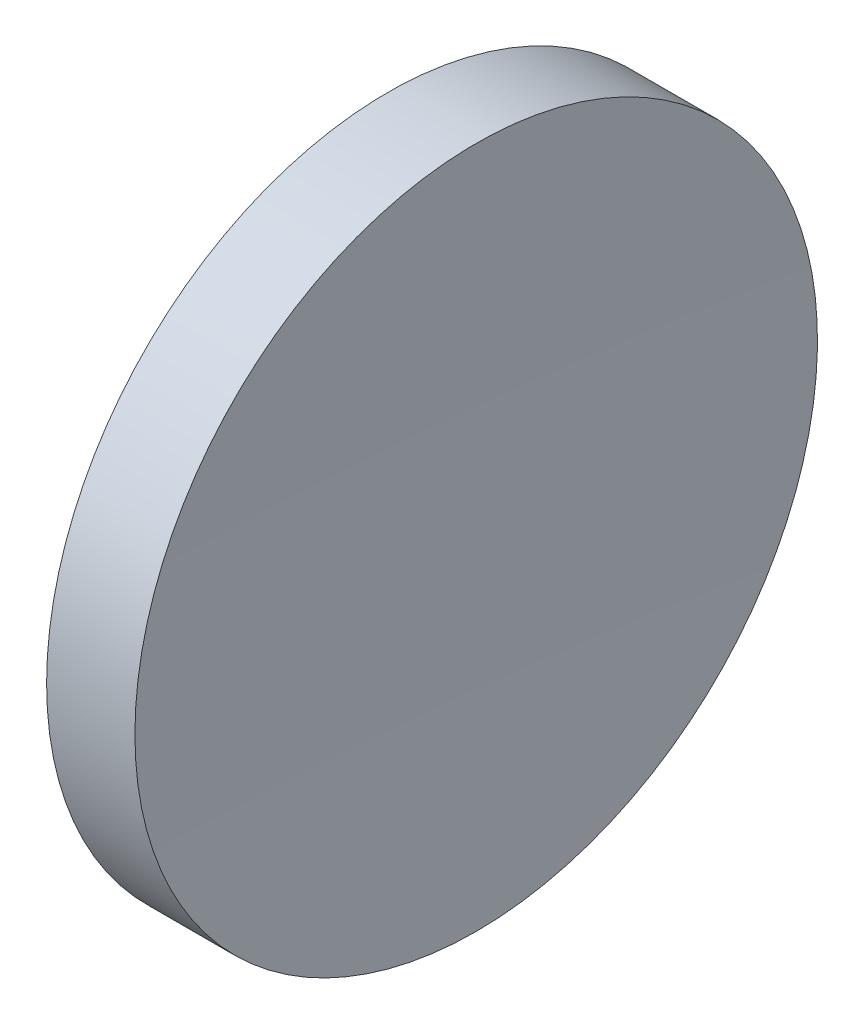
SolidWorks part; units mm, degrees
ref_plane "前视基准面" through (0, 0, 0) normal (0, 0, 1) x (1, 0, 0)
ref_plane "上视基准面" through (0, 0, 0) normal (0, 1, 0) x (1, 0, 0)
ref_plane "右视基准面" through (0, 0, 0) normal (1, 0, 0) x (0, 0, -1)
sketch "草图1" plane through (0, 0, 0) normal (0, 0, 1) x (1, 0, 0)
  line L0 (217.9703, 138.756) -> (265.5527, 138.756) construction
  line L1 (230.1996, 138.756) -> (230.1996, 176.256)
  line L2 (230.1996, 176.256) -> (239.903, 176.256)
  line L3 (239.1996, 138.756) -> (230.1996, 138.756)
  arc A0 (239.903, 176.256) -> (239.1996, 138.756) centre (1239.1996, 138.756) ccw
  dimension "D1" = 1000
  dimension "D2" = 9.7034
revolve "旋转1" add sketch "草图1" angle 360 about L0
